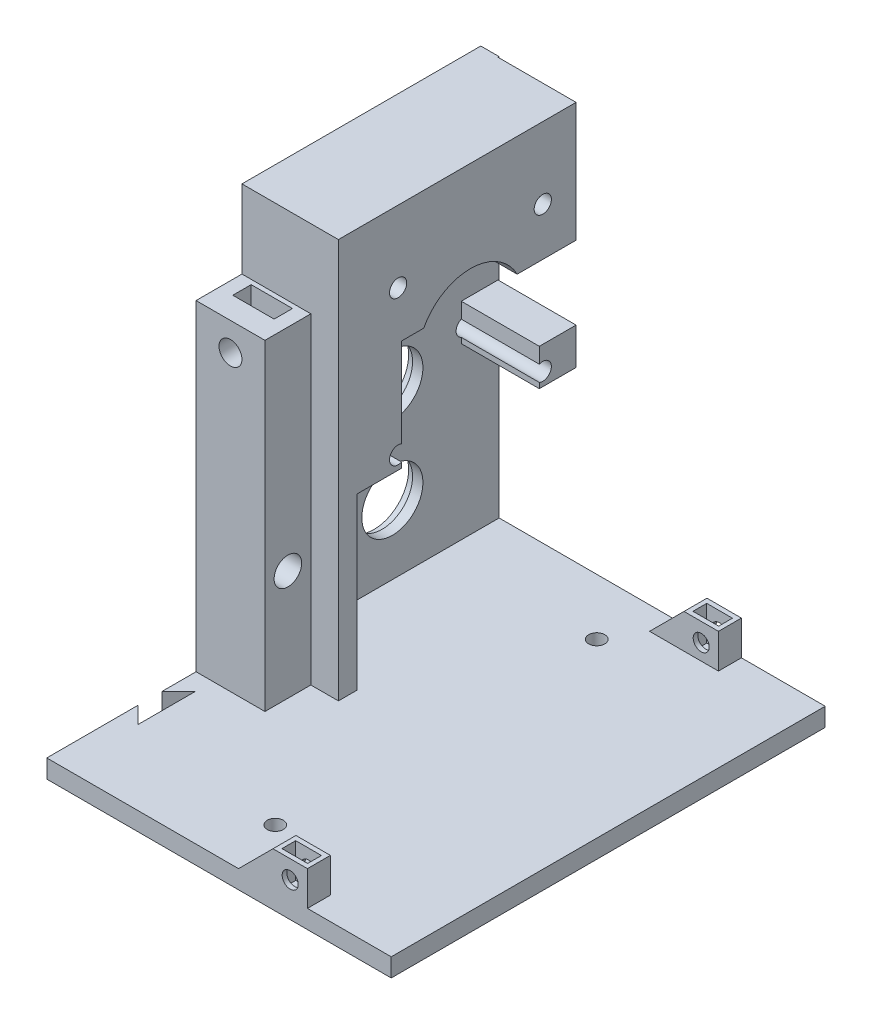
SolidWorks part; units mm, degrees
ref_plane "Front Plane" through (0, 0, 0) normal (0, 0, 1) x (1, 0, 0)
ref_plane "Top Plane" through (0, 0, 0) normal (0, 1, 0) x (1, 0, 0)
ref_plane "Right Plane" through (0, 0, 0) normal (1, 0, 0) x (0, 0, -1)
sketch "Sketch20" plane through (0, 0, 0) normal (0, 1, 0) x (1, 0, 0)
  line L1 (75, 0) -> (0, 0)
  line L2 (75, 0) -> (75, -94.5)
  line L3 (75, -94.5) -> (0, -94.5)
  line L4 (0, 0) -> (0, -94.5)
  dimension "D1" = 94.5
  dimension "D2" = 75
extrude "Base" add sketch "Sketch20" along normal blind 4 separate body
sketch "Sketch21" plane through (0, 4, 0) normal (0, 1, 0) x (1, 0, 0)
  line L0 (0, 0) -> (0, -94.5) construction
  line L1 (0, -52) -> (21, -52)
  line L2 (0, -52) -> (0, -48)
  line L3 (0, -48) -> (21, -48)
  line L4 (21, -52) -> (21, -48)
  line L6 (75, 0) -> (0, 0) construction
  dimension "D1" = 4
  dimension "D2" = 48
  dimension "D3" = 21
extrude "X_Wall" add sketch "Sketch21" along normal blind 87
sketch "Sketch22" plane through (0, 4, 0) normal (0, 1, 0) x (1, 0, 0)
  line L0 (75, 0) -> (0, 0) construction
  line L1 (0, -48) -> (4, -48)
  line L2 (0, -48) -> (0, 0)
  line L3 (0, 0) -> (4, 0)
  line L4 (4, -48) -> (4, 0)
  dimension "D1" = 4
extrude "Y_Wall" add sketch "Sketch22" along normal blind 87
sketch "Sketch23" plane through (0, 4, 0) normal (0, 1, 0) x (1, 0, 0)
  line L1 (0, -52) -> (15, -52)
  line L2 (0, -52) -> (0, -62)
  line L3 (0, -62) -> (15, -62)
  line L4 (15, -52) -> (15, -62)
  dimension "D1" = 15
  dimension "D2" = 10
extrude "Belt_Screw_Mount" add sketch "Sketch23" along normal blind 70
sketch "Sketch24" plane through (4, 0, 0) normal (1, 0, 0) x (0, 0, -1)
  line L0 (-48, 41) -> (-48, 91)
  line L1 (-48, 91) -> (-0.25, 91)
  line L2 (-0.25, 91) -> (-0.25, 41) construction
  line L3 (-0.25, 41) -> (-8.25, 41)
  line L4 (-8.25, 41) -> (-8.25, 65) construction
  line L5 (-8.25, 65) -> (-38.25, 65)
  line L6 (-38.25, 65) -> (-38.25, 41)
  line L7 (-38.25, 41) -> (-48, 41)
  line L8 (-48, 91) -> (0, 91) construction
  line L11 (-48, 91) -> (-48, 4) construction
  line L13 (-8.25, 41) -> (-8.25, 49)
  line L14 (-0.25, 41) -> (-0.25, 49)
  line L16 (-0.25, 49) -> (-8.25, 49)
  line L17 (-8.25, 65) -> (-0.25, 65)
  line L18 (-0.25, 91) -> (-0.25, 65)
  point P10 (-23.25, 65)
  dimension "D1" = 30
  dimension "D2" = 24
  dimension "D3" = 26
  dimension "D4" = 8
  dimension "D5" = 24.75
  dimension "D6" = 8
extrude "Motor_Spacer" add sketch "Sketch24" along normal blind 17
sketch "Sketch14" plane through (0, 0, 0) normal (-1, 0, 0) x (0, 0, 1)
  line L0 (23.25, 40.65) -> (23.25, 19) construction
  line L2 (23.25, 40.65) -> (23.25, 59.65) construction
  line L3 (7.5, 43.9) -> (39, 43.9) construction
  line L4 (7.5, 43.9) -> (39, 75.4) construction
  line L5 (39, 43.9) -> (7.5, 75.4) construction
  line L6 (7.5, 75.4) -> (39, 75.4) construction
  line L8 (0, 0) -> (94.5, 0) construction
  line L9 (52, 91) -> (52, 74) construction
  circle A0 centre (23.25, 19) radius 6.65
  circle A1 centre (23.25, 40.65) radius 6.65
  circle A2 centre (23.25, 59.65) radius 3.75
  circle A3 centre (39, 75.4) radius 1.875
  circle A4 centre (39, 43.9) radius 1.875
  circle A5 centre (7.5, 43.9) radius 1.875
  circle A6 centre (7.5, 75.4) radius 1.875
  point P18 (23.25, 59.65)
  dimension "D1" = 21.65
  dimension "D2" = 13.3
  dimension "D3" = 13.3
  dimension "D6" = 7.5
  dimension "D7" = 3.75
  dimension "D8" = 3.75
  dimension "D9" = 3.75
  dimension "D10" = 3.75
  dimension "D4" = 19
  dimension "D5" = 19
  dimension "D11" = 31.5
  dimension "D12" = 31.5
  dimension "D13" = 31.5
  dimension "D14" = 31.5
  dimension "D15" = 13
extrude "Motor_Bearing_Holes" cut sketch "Sketch14" against normal blind 21
sketch "Sketch15" plane through (0, 0, 0) normal (-1, 0, 0) x (0, 0, 1)
  circle A0 centre (23.25, 19) radius 7.55
  circle A1 centre (23.25, 40.65) radius 7.55
  circle A4 centre (23.25, 40.65) radius 6.65 construction
  circle A5 centre (23.25, 19) radius 6.65 construction
  dimension "D1" = 15.1
  dimension "D2" = 15.1
extrude "Bearing_Holes_2" cut sketch "Sketch15" against normal blind 1.75
sketch "Sketch17" plane through (0, 0, 62) normal (0, 0, 1) x (1, 0, 0)
  line L3 (7.5, 74) -> (7.5, 67.9) construction
  line L4 (0, 74) -> (15, 74) construction
  circle A0 centre (7.5, 67.9) radius 2.5
  dimension "D1" = 5
  dimension "D2" = 6.1
extrude "Belt_Screw_Hole" cut sketch "Sketch17" against normal blind 8
sketch "Sketch18" plane through (0, 74, 0) normal (0, 1, 0) x (1, 0, 0)
  line L0 (0, -57) -> (15, -57) construction
  line L1 (3, -53) -> (12, -53)
  line L2 (3, -53) -> (3, -57)
  line L3 (3, -57) -> (12, -57)
  line L4 (12, -53) -> (12, -57)
  line L10 (0, -52) -> (0, -62) construction
  line L11 (15, -62) -> (15, -52) construction
  point P7 (7.5, -57)
  point P11 (7.5, -57)
  point P13 (7.5, -57)
  dimension "D1" = 4
  dimension "D2" = 9
extrude "Belt_Bolt_Hole" cut sketch "Sketch18" against normal blind 10.35
sketch "Sketch25" plane through (21, 0, 0) normal (1, 0, 0) x (0, 0, -1)
  circle A0 centre (-23.25, 59.65) radius 11.5
  dimension "D1" = 23
extrude "Motor_Cutout" cut sketch "Sketch25" against normal blind 17
sketch "Sketch26" plane through (0, 0, 0) normal (-1, 0, 0) x (0, 0, 1)
  line L0 (52, 74) -> (52, 0) construction
  line L1 (0, 0) -> (94.5, 0) construction
  line L4 (57, 28) -> (52, 28)
  line L6 (57, 28) -> (57, 0) construction
  circle A0 centre (57, 28) radius 1.75
  dimension "D1" = 5
  dimension "D2" = 28
extrude "Connector_Screw-hole" cut sketch "Sketch26" against normal blind 15
sketch "Sketch42" plane through (15, 0, 0) normal (1, 0, 0) x (0, 0, -1)
  circle A0 centre (-57, 28) radius 3
  dimension "D1" = 6
extrude "Cut-Extrude2" cut sketch "Sketch42" against normal blind 7
sketch "Sketch27" plane through (0, 0, 0) normal (0, -1, 0) x (1, 0, 0)
  line L0 (0, 47.25) -> (75, 47.25) construction
  line L1 (0, 0) -> (0, 94.5) construction
  line L2 (75, 94.5) -> (75, 0) construction
  line L3 (0, 47.25) -> (0, 72) construction
  line L4 (0, 69.5) -> (0, 74.5) construction
  line L8 (0, 74.5) -> (3.5355, 78.0355) construction
  line L9 (3.5355, 78.0355) -> (3.5355, 65.9645) construction
  line L10 (3.5355, 65.9645) -> (0, 69.5) construction
  line L15 (3.6355, 65.723) -> (-0.1, 69.4586)
  line L16 (-0.1, 69.4586) -> (-0.1, 74.5414)
  line L17 (-0.1, 74.5414) -> (3.6355, 78.277)
  line L18 (3.6355, 78.277) -> (3.6355, 65.723)
  line L19 (3.6355, 16.223) -> (3.6355, 28.777)
  line L20 (-0.1, 19.9586) -> (3.6355, 16.223)
  line L21 (-0.1, 25.0414) -> (-0.1, 19.9586)
  line L22 (3.6355, 28.777) -> (-0.1, 25.0414)
  point P10 (0, 72)
  dimension "D1" = 20
  dimension "D2" = 5
  dimension "D3" = 5
  dimension "D4" = 5
  dimension "D5" = 45
  dimension "D6" = 0.1
extrude "DoveTailCutout" cut sketch "Sketch27" against normal blind 4.2
sketch "Sketch28" plane through (0, 0, 94.5) normal (0, 0, 1) x (1, 0, 0)
  line L0 (56.75, 4) -> (56.75, 11.5)
  line L1 (56.75, 11.5) -> (49.25, 11.5)
  line L2 (49.25, 11.5) -> (41.75, 4)
  line L3 (41.75, 4) -> (56.75, 4)
  line L4 (75, 4) -> (75, 0) construction
  line L6 (0, 4) -> (75, 4) construction
  dimension "D1" = 7.5
  dimension "D2" = 7.5
  dimension "D3" = 45
  dimension "D4" = 18.25
extrude "Front_Right_Case_Screw_Body" add sketch "Sketch28" against normal blind 5
sketch "Sketch29" plane through (0, 0, 94.5) normal (0, 0, 1) x (1, 0, 0)
  line L0 (56.75, 4) -> (56.75, 11.5) construction
  line L4 (0, 0) -> (75, 0) construction
  circle A0 centre (53, 7.5) radius 1.75
  dimension "D1" = 3.5
  dimension "D2" = 3.75
  dimension "D3" = 7.5
extrude "Front_Right_Case_Screw_Hole" cut sketch "Sketch29" against normal blind 10
sketch "Sketch30" plane through (0, 11.5, 0) normal (0, 1, 0) x (1, 0, 0)
  line L0 (56.75, -94.5) -> (49.25, -94.5) construction
  line L1 (50.2, -90.5) -> (55.8, -90.5)
  line L2 (50.2, -90.5) -> (50.2, -93.5)
  line L3 (50.2, -93.5) -> (55.8, -93.5)
  line L4 (55.8, -90.5) -> (55.8, -93.5)
  line L5 (56.75, -89.5) -> (56.75, -94.5) construction
  point P6 (53, -93.5)
  dimension "D1" = 3
  dimension "D2" = 5.6
  dimension "D3" = 1
  dimension "D4" = 3.75
extrude "Front_Right_Case_Nut_Hole" cut sketch "Sketch30" against normal blind 7.5
ref_plane "Right_Front_Case_Screw_Plane" through (0, 0, 80.75) normal (0, 0, 1) x (1, 0, 0)
sketch "Sketch31" plane through (0, 0, 80.75) normal (0, 0, 1) x (1, 0, 0)
  line L0 (75, 4) -> (75, 11.5)
  line L1 (75, 11.5) -> (70, 11.5)
  line L2 (70, 11.5) -> (62.5, 4)
  line L3 (62.5, 4) -> (75, 4)
  line L5 (0, 4) -> (41.75, 4) construction
  line L6 (75, 4) -> (75, 0) construction
  dimension "D1" = 5
  dimension "D2" = 7.5
  dimension "D3" = 45
extrude "Right_Front_Case_Screw_Body" [suppressed] add sketch "Sketch31" against normal blind 7.5
sketch "Sketch32" [suppressed] plane through (75, 0, 0) normal (1, 0, 0) x (0, 0, -1)
  line L0 (-73.25, 7.5) -> (-80.75, 7.5) construction
  line L1 (-73.25, 4) -> (-73.25, 11.5) construction
  line L2 (-80.75, 6.325) -> (-80.75, -6.325) construction
  line L3 (-94.5, 0) -> (0, 0) construction
  circle A0 centre (-77, 7.5) radius 1.75
  point P11 (-77, 7.5)
  dimension "D1" = 3.5
  dimension "D2" = 7.5
extrude "Right_Front_Case_Screw_Hole" [suppressed] cut sketch "Sketch32" against normal blind 9
sketch "Sketch33" [suppressed] plane through (0, 11.5, 0) normal (0, 1, 0) x (1, 0, 0)
  line L0 (74, -80.75) -> (74, -73.25) construction
  line L1 (71, -74.2) -> (74, -74.2)
  line L2 (71, -74.2) -> (71, -79.8)
  line L3 (71, -79.8) -> (74, -79.8)
  line L4 (74, -74.2) -> (74, -79.8)
  line L8 (75, -80.75) -> (70, -80.75) construction
  line L9 (75, -73.25) -> (70, -73.25) construction
  line L10 (75, -73.25) -> (75, -80.75) construction
  point P12 (74, -77)
  point P13 (74, -77)
  dimension "D1" = 3
  dimension "D2" = 5.6
  dimension "D3" = 1
extrude "Right_Front_Case_Nut_Hole" [suppressed] cut sketch "Sketch33" against normal blind 7.5
ref_plane "Plane2" through (0, 0, 10.75) normal (0, 0, -1) x (-1, 0, 0)
sketch "Sketch34" plane through (0, 0, 10.75) normal (0, 0, -1) x (-1, 0, 0)
  line L0 (-75, 4) -> (-75, 11.5)
  line L1 (-75, 11.5) -> (-70, 11.5)
  line L2 (-70, 11.5) -> (-62.5, 4)
  line L3 (-62.5, 4) -> (-75, 4)
  line L4 (0, 4) -> (-41.75, 4) construction
  line L5 (-75, 4) -> (-75, 0) construction
  dimension "D1" = 45
  dimension "D2" = 5
  dimension "D3" = 7.5
extrude "Right_Back_Case_Screw_Body" [suppressed] add sketch "Sketch34" against normal blind 7.5
sketch "Sketch35" [suppressed] plane through (75, 0, 0) normal (1, 0, 0) x (0, 0, -1)
  line L0 (-10.75, 7.5) -> (-18.25, 7.5) construction
  line L1 (-10.75, 11.5) -> (-10.75, 4) construction
  line L2 (-18.25, 11.5) -> (-18.25, 4) construction
  line L3 (-94.5, 0) -> (0, 0) construction
  circle A0 centre (-14.5, 7.5) radius 1.75
  point P11 (-14.5, 7.5)
  dimension "D1" = 3.5
  dimension "D2" = 7.5
extrude "Right_Back_Case_Screw_Hole" [suppressed] cut sketch "Sketch35" against normal blind 9
sketch "Sketch36" [suppressed] plane through (0, 11.5, 0) normal (0, 1, 0) x (1, 0, 0)
  line L0 (74, -18.25) -> (74, -10.75) construction
  line L1 (71, -11.7) -> (74, -11.7)
  line L2 (71, -11.7) -> (71, -17.3)
  line L3 (71, -17.3) -> (74, -17.3)
  line L4 (74, -11.7) -> (74, -17.3)
  line L5 (75, -18.25) -> (62.5, -18.25) construction
  line L6 (70, -10.75) -> (75, -10.75) construction
  line L7 (75, -18.25) -> (75, -10.75) construction
  point P12 (74, -14.5)
  point P13 (74, -14.5)
  dimension "D1" = 5.6
  dimension "D2" = 3
  dimension "D3" = 1
extrude "Right_Back_Case_Nut_Hole" [suppressed] cut sketch "Sketch36" against normal blind 7.5
sketch "Sketch37" plane through (0, 0, 0) normal (0, 0, -1) x (-1, 0, 0)
  line L0 (-56.75, 4) -> (-56.75, 11.5)
  line L1 (-21, 4) -> (-4, 4) construction
  line L2 (-56.75, 11.5) -> (-49.25, 11.5)
  line L3 (-49.25, 11.5) -> (-41.75, 4)
  line L4 (-41.75, 4) -> (-56.75, 4)
  line L5 (-75, 4) -> (-75, 0) construction
  dimension "D1" = 7.5
  dimension "D2" = 7.5
  dimension "D3" = 45
  dimension "D4" = 18.25
extrude "Back_Right_Case_Screw_Body" add sketch "Sketch37" against normal blind 5 separate body
sketch "Sketch38" plane through (0, 0, 0) normal (0, 0, -1) x (-1, 0, 0)
  line L5 (-75, 0) -> (0, 0) construction
  line L6 (-56.75, 11.5) -> (-56.75, 4) construction
  circle A0 centre (-53, 7.5) radius 1.75
  dimension "D1" = 3.5
  dimension "D2" = 3.75
  dimension "D3" = 7.5
extrude "Back_Right_Case_Screw_Hole" cut sketch "Sketch38" against normal blind 5
sketch "Sketch39" plane through (0, 11.5, 0) normal (0, 1, 0) x (1, 0, 0)
  line L0 (49.25, -1) -> (56.75, -1) construction
  line L1 (50.2, -1) -> (55.8, -1)
  line L2 (50.2, -1) -> (50.2, -4)
  line L3 (50.2, -4) -> (55.8, -4)
  line L4 (55.8, -1) -> (55.8, -4)
  line L5 (49.25, -5) -> (49.25, 0) construction
  line L6 (56.75, -5) -> (56.75, 0) construction
  line L7 (49.25, 0) -> (56.75, 0) construction
  point P12 (53, -1)
  point P13 (53, -1)
  dimension "D1" = 5.6
  dimension "D2" = 3
  dimension "D3" = 1
extrude "Back_Right_Case_Nut_Hole" cut sketch "Sketch39" against normal blind 7.5
sketch "Sketch40" plane through (0, 0, 0) normal (0, -1, 0) x (1, 0, 0)
  line L0 (37.5, 94.5) -> (37.5, 82.25) construction
  line L1 (0, 94.5) -> (75, 94.5) construction
  line L2 (37.5, 82.25) -> (37.5, 47.25) construction
  line L3 (37.5, 47.25) -> (37.5, 12.25) construction
  line L4 (37.5, 12.25) -> (37.5, 0) construction
  line L5 (75, 0) -> (0, 0) construction
  circle A0 centre (37.5, 82.25) radius 1.75
  circle A1 centre (37.5, 12.25) radius 1.75
  dimension "D1" = 3.5
  dimension "D2" = 3.5
  dimension "D3" = 35
extrude "Foot_Holes" cut sketch "Sketch40" against normal blind 10
sketch "Sketch41" plane through (4, 0, 0) normal (1, 0, 0) x (0, 0, -1)
  line L0 (-41.83, 4) -> (-35.83, 4)
  line L1 (-48, 4) -> (0, 4) construction
  line L2 (-35.83, 4) -> (-35.83, 26)
  line L5 (-41.83, 26) -> (-41.83, 4)
  line L7 (-41.83, 26) -> (-35.83, 26)
  line L8 (-48, 11) -> (-44.915, 11) construction
  line L9 (-48, 41) -> (-48, 4) construction
  line L10 (-44.915, 11) -> (-41.83, 11) construction
  line L11 (-44.915, 11) -> (-44.915, 6) construction
  circle A0 centre (-44.915, 11) radius 1.5
  circle A1 centre (-44.915, 6) radius 1.5
  point P4 (-38.83, 4)
  dimension "D3" = 3
  dimension "D5" = 3
  dimension "D1" = 6
  dimension "D2" = 22
  dimension "D4" = 9.17
  dimension "D6" = 2
  dimension "D7" = 5
extrude "Motor_Cable_Passthrough" cut sketch "Sketch41" against normal up to next (4 mm away)
